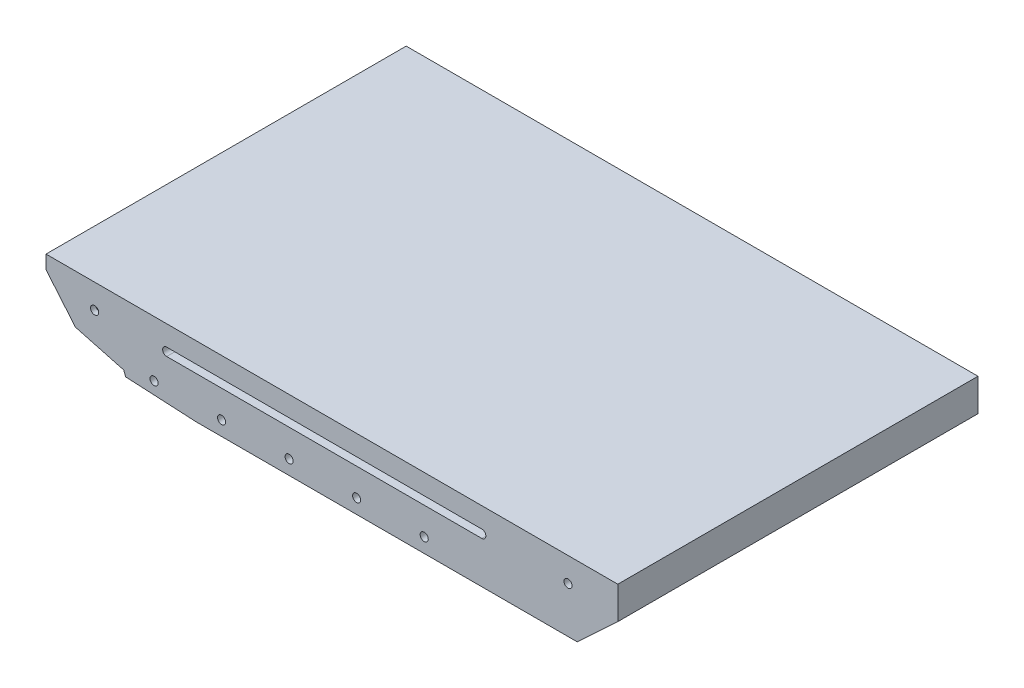
SolidWorks part; units mm, degrees
ref_plane "Front Plane" through (0, 0, 0) normal (0, 0, 1) x (1, 0, 0)
ref_plane "Top Plane" through (0, 0, 0) normal (0, 1, 0) x (1, 0, 0)
ref_plane "Right Plane" through (0, 0, 0) normal (1, 0, 0) x (0, 0, -1)
sketch "Sketch1" plane through (0, 0, 0) normal (0, 0, 1) x (1, 0, 0)
  line L0 (295, 0) -> (340, 41.9632)
  line L1 (-295, 78) -> (340, 78)
  line L2 (-295, 78) -> (-295, 0)
  line L3 (-295, 0) -> (295, 0)
  line L4 (340, 78) -> (340, 41.9632)
  point P1 (0, 0)
  dimension "D1" = 635
  dimension "D2" = 78
  dimension "D3" = 43
  dimension "D4" = 45
extrude "Boss-Extrude1" add sketch "Sketch1" along normal mid plane 400 contours L1 L4 L0 L3 L2
sketch "Sketch2" plane through (0, 0, 200) normal (0, 0, 1) x (1, 0, 0)
  line L0 (-295, 63) -> (-295, 78)
  line L1 (-295, 78) -> (-295, 0) construction
  line L2 (-295, 78) -> (340, 78) construction
  line L3 (-295, 78) -> (-295, 63)
  line L4 (-295, 63) -> (-247.3868, 6.2568)
  line L5 (-247.3868, 6.2568) -> (-128, 0)
  line L6 (-295, 0) -> (295, 0) construction
  line M4 (-295, 78) -> (-295, 0)
  line M5 (-295, 0) -> (295, 0)
  dimension "D1" = 15
  dimension "D2" = 40
  dimension "D3" = 3
  dimension "D4" = 423
extrude "Cut-Extrude1" cut sketch "Sketch2" against normal blind 1875 contours L5 L4 M4 M5
sketch "Sketch3" plane through (0, 0, 200) normal (0, 0, 1) x (1, 0, 0)
  line L0 (-206.5, 4.114) -> (-208.7476, 9.6771)
  line L1 (-247.3868, 6.2568) -> (-128, 0) construction
  line L2 (-208.7476, 9.6771) -> (-262.2751, 24)
  line L3 (-295, 63) -> (-247.3868, 6.2568) construction
  line L5 (-295, 78) -> (340, 78) construction
  dimension "D1" = 54
  dimension "D2" = 6
  dimension "D3" = 115
  dimension "D4" = 78.5
extrude "Cut-Extrude2" cut sketch "Sketch3" against normal through all and the other way through all
sketch "Sketch9" plane through (0, 0, 0) normal (0, 0, 1) x (1, 0, 0)
  line L0 (-128, 0) -> (295, 0) construction
  line L1 (-295, 78) -> (-295, 63) construction
  line L2 (-295, 78) -> (340, 78) construction
  line L3 (340, 78) -> (340, 41.9632) construction
  line L4 (-161, 51) -> (189, 51) construction
  line L5 (-161, 55.5) -> (189, 55.5)
  line L6 (-161, 46.5) -> (189, 46.5)
  circle A0 centre (-175, 16) radius 4.5
  circle A1 centre (-100, 16) radius 4.5
  circle A2 centre (-25, 16) radius 4.5
  circle A3 centre (50, 16) radius 4.5
  circle A4 centre (125, 16) radius 4.5
  circle A5 centre (-241, 51) radius 4.5
  circle A7 centre (284.7, 51) radius 4.5
  arc A8 (-161, 55.5) -> (-161, 46.5) centre (-161, 51) ccw
  arc A9 (189, 46.5) -> (189, 55.5) centre (189, 51) ccw
  point P22 (14, 51)
  dimension "D1" = 9
  dimension "D3" = 120
  dimension "D4" = 9
  dimension "D5" = 54
  dimension "D6" = 27
  dimension "D7" = 4.5
  dimension "D9" = 9
  dimension "D2" = 16
  dimension "D8" = 80
  dimension "D10" = 55.3
  dimension "D11" = 350
extrude "Cut-Extrude8" cut sketch "Sketch9" against normal mid plane 1070
sketch "Sketch10" plane through (0, 0, 0) normal (0, 1, 0) x (1, 0, 0)
  line L1 (-119.3067, -190.7883) -> (288.302, -190.7883)
  line L2 (-119.3067, -190.7883) -> (-119.3067, 192.8435)
  line L3 (-119.3067, 192.8435) -> (288.302, 192.8435)
  line L4 (288.302, -190.7883) -> (288.302, 192.8435)
extrude "Cut-Extrude9" cut sketch "Sketch10" along normal blind 40
sketch "Sketch11" plane through (0, 40, 0) normal (0, -1, 0) x (1, 0, 0)
  line L0 (-208.7476, 200) -> (-208.7476, -200) construction
  line L1 (268.4354, -155.1653) -> (322.5548, -155.1653)
  line L2 (268.4354, -155.1653) -> (268.4354, -189.4182)
  line L3 (268.4354, -189.4182) -> (322.5548, -189.4182)
  line L4 (322.5548, -155.1653) -> (322.5548, -189.4182)
  line L5 (-257.0031, -155.1653) -> (-208.7476, -155.1653)
  line L6 (-257.0031, -155.1653) -> (-257.0031, -194.2136)
  line L7 (-257.0031, -194.2136) -> (-208.7476, -194.2136)
  line L8 (-208.7476, -155.1653) -> (-208.7476, -194.2136)
  line L9 (42.9, 0) -> (-42.9, 0) construction
  line L10 (322.5548, 155.1653) -> (322.5548, 189.4182)
  line L11 (268.4354, 189.4182) -> (322.5548, 189.4182)
  line L12 (268.4354, 155.1653) -> (322.5548, 155.1653)
  line L13 (268.4354, 155.1653) -> (268.4354, 189.4182)
  line L14 (-208.7476, 155.1653) -> (-208.7476, 194.2136)
  line L15 (-257.0031, 194.2136) -> (-208.7476, 194.2136)
  line L16 (-257.0031, 155.1653) -> (-257.0031, 194.2136)
  line L17 (-257.0031, 155.1653) -> (-208.7476, 155.1653)
extrude "Cut-Extrude10" cut sketch "Sketch11" against normal mid plane 50 contours L6 L5 L8 L7 | L2 L3 L4 L1 | L14 L15 L16 L17 | L10 L11 L13 L12
